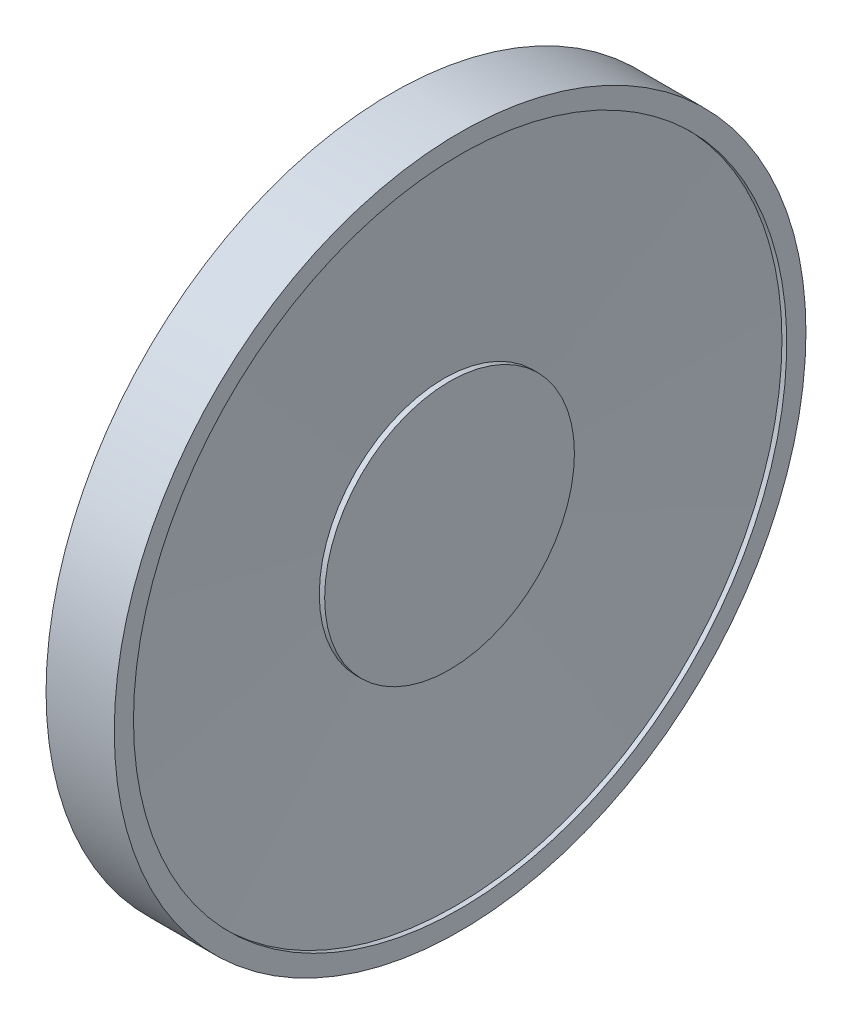
SolidWorks part; units mm, degrees
ref_plane "Front Plane" through (0, 0, 0) normal (0, 0, 1) x (1, 0, 0)
ref_plane "Top Plane" through (0, 0, 0) normal (0, 1, 0) x (1, 0, 0)
ref_plane "Right Plane" through (0, 0, 0) normal (1, 0, 0) x (0, 0, -1)
sketch "Sketch2" plane through (0, 0, 0) normal (1, 0, 0) x (0, 0, -1)
  circle A0 centre (0, 0) radius 8.75
  dimension "D1" = 17.5
extrude "Boss-Extrude2" add sketch "Sketch2" along normal blind 3.5
ref_plane "Plane1" through (0.5, 0, 0) normal (-1, 0, 0) x (0, 0, 1)
sketch "Sketch3" plane through (0.5, 0, 0) normal (-1, 0, 0) x (0, 0, 1)
  circle A0 centre (0, 0) radius 16.5
  dimension "D1" = 33
extrude "Boss-Extrude3" add sketch "Sketch3" against normal blind 1.5
ref_plane "Plane2" through (1.25, 0, 0) normal (1, 0, 0) x (0, 0, -1)
ref_plane "Plane3" through (4.8, 0, 0) normal (-1, 0, 0) x (0, 0, 1)
sketch "Sketch5" plane through (1.25, 0, 0) normal (1, 0, 0) x (0, 0, -1)
  circle A0 centre (0, 0) radius 18
  circle A1 centre (0, 0) radius 17
  dimension "D1" = 36
  dimension "D2" = 1
extrude "Boss-Extrude4" add sketch "Sketch5" along normal up to surface (3.55 mm away) separate body up to plane "Plane3"
sketch "Sketch6" plane through (1.25, 0, 0) normal (1, 0, 0) x (0, 0, -1)
  circle A1 centre (0, 0) radius 17
  circle A2 centre (0, 0) radius 15
  circle A3 centre (0, 0) radius 15
  dimension "D1" = 3
  dimension "D2" = 2
extrude "Boss-Extrude5" add sketch "Sketch6" along normal blind 1.5
ref_plane "Plane4" through (4.3, 0, 0) normal (1, 0, 0) x (0, 0, -1)
sketch "Sketch8" plane through (3.5, 0, 0) normal (1, 0, 0) x (0, 0, -1)
  circle A0 centre (0, 0) radius 6.5
  dimension "D1" = 13
extrude "Boss-Extrude6" add sketch "Sketch8" along normal blind 0.75
sketch "Sketch10" plane through (0, 0, 0) normal (0, 1, 0) x (1, 0, 0)
  line L0 (1.25, 0) -> (3.6112, 0)
  line L1 (1.25, -16.5) -> (1.25, 16.5) construction
  line L2 (3.6112, 0) -> (4.55, 17)
  line L3 (4.8, 17) -> (2.75, 17) construction
  line L4 (4.55, 17) -> (2.75, 17)
  line L5 (2.75, 17) -> (1.25, 0)
  line L6 (4.8, -17) -> (4.8, 17) construction
  dimension "D1" = 0.25
revolve "Revolve1" add sketch "Sketch10" angle 360 about L0
sketch "Sketch11" plane through (0.5, 0, 0) normal (-1, 0, 0) x (0, 0, 1)
  line L0 (8.25, -14.2894) -> (4.375, -7.5777)
  line L1 (-4.375, -7.5777) -> (-8.25, -14.2894)
  arc A0 (-8.25, -14.2894) -> (8.25, -14.2894) centre (0, 0) ccw
  circle A1 centre (0, 0) radius 16.5 construction
  arc A2 (-4.375, -7.5777) -> (4.375, -7.5777) centre (0, 0) ccw
  circle A3 centre (0, 0) radius 8.75 construction
  dimension "D1" = 60
extrude "Boss-Extrude7" add sketch "Sketch11" along normal blind 0.4
ref_plane "Plane5" through (0, 0, 0) normal (0, 1, 0) x (1, 0, 0)
